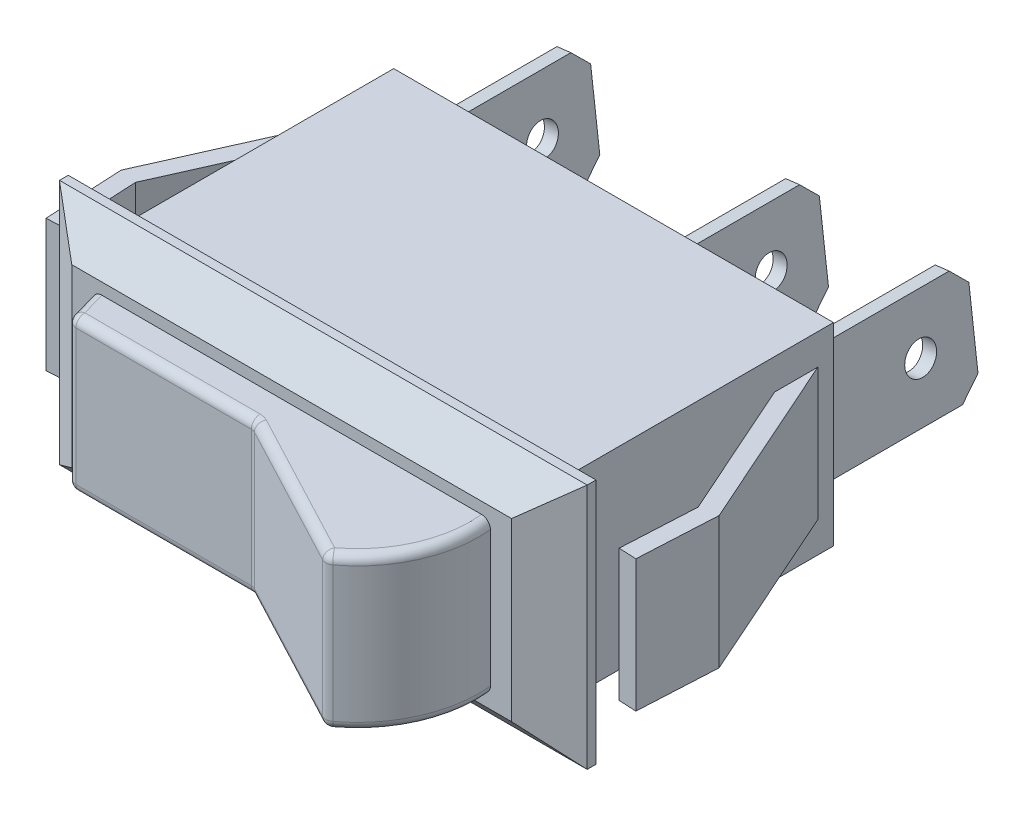
SolidWorks part; units mm, degrees
ref_plane "Front Plane" through (0, 0, 0) normal (0, 0, 1) x (1, 0, 0)
ref_plane "Top Plane" through (0, 0, 0) normal (0, 1, 0) x (1, 0, 0)
ref_plane "Right Plane" through (0, 0, 0) normal (1, 0, 0) x (0, 0, -1)
sketch "Sketch1" plane through (0, 0, 0) normal (0, 0, 1) x (1, 0, 0)
  line L1 (0, 0) -> (25, 0)
  line L2 (0, 0) -> (0, 11)
  line L3 (0, 11) -> (25, 11)
  line L4 (25, 0) -> (25, 11)
  dimension "D1" = 25
  dimension "D2" = 11
extrude "Extrude1" add sketch "Sketch1" along normal blind 16
sketch "Sketch2" plane through (0, 0, 16) normal (0, 0, 1) x (1, 0, 0)
  line L0 (0, 0) -> (25, 0) construction
  line L1 (-2.5, -1.5) -> (27.5, -1.5)
  line L2 (-2.5, -1.5) -> (-2.5, 12.5)
  line L3 (-2.5, 12.5) -> (27.5, 12.5)
  line L4 (27.5, -1.5) -> (27.5, 12.5)
  line L5 (0, 11) -> (0, 0) construction
  dimension "D1" = 30
  dimension "D2" = 14
  dimension "D3" = 1.5
  dimension "D4" = 2.5
extrude "Extrude2" add sketch "Sketch2" along normal blind 2.3
chamfer "Chamfer1" distance 1.8 distance2 2 2 edges at (12.5, 12.5, 18.3) (12.5, -1.5, 18.3)
chamfer "Chamfer2" distance 1.8 distance2 2.5 2 edges at (27.5, 5.5, 18.3) (-2.5, 5.5, 18.3)
ref_plane "Plane1" through (0, 5.5, 0) normal (0, 1, 0) x (-1, 0, 0)
sketch "Sketch4" plane through (0, 5.5, 0) normal (0, 1, 0) x (-1, 0, 0)
  line L0 (0, 0.8928) -> (4.5, 11)
  line L1 (0, 16) -> (0, 0) construction
  line L2 (4.5, 11) -> (4.2642, 15.5)
  line L3 (-25, 0) -> (0, 0) construction
  line L4 (0, 3.3514) -> (3.4888, 11.1874)
  line L5 (3.4888, 11.1874) -> (3.2655, 15.4477)
  line L6 (4.2642, 15.5) -> (3.2655, 15.4477)
  line L7 (0, 0.8928) -> (0, 3.3514)
  line L8 (-0.9135, 1.2996) -> (3.4888, 11.1874) construction
  dimension "D1" = 11
  dimension "D2" = 4.5
  dimension "D3" = 246
  dimension "D4" = 273
  dimension "D5" = 15.5
  dimension "D6" = 1
extrude "Extrude3" add sketch "Sketch4" along normal blind 3.75 and the other way blind 3.75
ref_plane "Plane2" through (12.5, 0, 0) normal (1, 0, 0) x (0, 0, -1)
mirror "Mirror1" about plane through (12.5, 0, 0) normal (1, 0, 0) of "Extrude3"
sketch "Sketch6" plane through (0, 5.5, 0) normal (0, 1, 0) x (-1, 0, 0)
  line L0 (-1.2, 18.3) -> (-1.7107, 20.15)
  line L1 (-25, 18.3) -> (0, 18.3) construction
  line L2 (-1.7107, 20.15) -> (-12.1809, 20.15)
  line L3 (-12.1809, 20.15) -> (-20.7938, 24.7)
  line L4 (-23.8, 18.3) -> (-1.2, 18.3)
  line L5 (-12.5, 6.05) -> (-12.5, -6.05) construction
  line L6 (-25, 16) -> (0, 16) construction
  arc A0 (-20.7938, 24.7) -> (-23.8, 18.3) centre (-16.9254, 18.9769) ccw
  dimension "D1" = 22.6
  dimension "D2" = 11.3
  dimension "D3" = 4.15
  dimension "D4" = 8.7
extrude "Extrude4" add sketch "Sketch6" along normal blind 4.35 and the other way blind 4.35
fillet "Fillet1" radius 0.5 11 edges at (16.4873, 9.85, 22.425) (16.4873, 1.15, 22.425) (23.1778, 1.15, 21.9138) (23.1778, 9.85, 21.9138) (20.7938, 5.5, 24.7) (12.1809, 5.5, 20.15) (6.9458, 1.15, 20.15) (1.4554, 1.15, 19.225) (6.9458, 9.85, 20.15) (1.4554, 9.85, 19.225) (1.7107, 5.5, 20.15)
sketch "Sketch7" plane through (0, 0, 0) normal (0, -1, 0) x (1, 0, 0)
  line L0 (25, 16) -> (25, 0) construction
  line L1 (25, 7.5) -> (0, 7.5)
  line L2 (25, 7.5) -> (25, 5)
  line L3 (25, 5) -> (0, 5)
  line L4 (0, 7.5) -> (0, 5)
  line L5 (0, 16) -> (0, 0) construction
  line L6 (0, 0) -> (25, 0) construction
  dimension "D1" = 2.5
  dimension "D2" = 5
extrude "Cut-Extrude2" cut sketch "Sketch7" against normal blind 0.44
ref_plane "Plane3" through (0, 0, 0) normal (0.9925, 0.1219, 0) x (0, 0, -1)
ref_plane "Plane4" through (1.9851, 0.2437, 0) normal (0.9925, 0.1219, 0) x (0, 0, -1)
sketch "Sketch8" plane through (1.9851, 0.2437, 0) normal (0.9925, 0.1219, 0) x (0, 0, -1)
  line L0 (8.3, 1.9928) -> (9.3, 2.9928)
  line L1 (0.5, 1.9928) -> (8.3, 1.9928)
  line L2 (0, 2.4928) -> (0, 7.7428)
  line L3 (0.5, 8.2428) -> (8.3, 8.2428)
  line L4 (9.3, 2.9928) -> (9.3, 7.2428)
  line L5 (8.3, 8.2428) -> (9.3, 7.2428)
  line L6 (0, 2.4928) -> (0.5, 1.9928)
  line L7 (0, 7.7428) -> (0.5, 8.2428)
  circle A0 centre (6.3, 5.1178) radius 0.9
  point P0 (0, 1.9928)
  point P1 (9.3, 8.2428)
  point P2 (0, 8.2428)
  point P3 (9.3, 1.9928)
  dimension "D3" = 1.8
  dimension "D1" = 9.3
  dimension "D2" = 6.25
  dimension "D4" = 3.125
  dimension "D7" = 3
extrude "Extrude5" add sketch "Sketch8" along normal blind 0.8
pattern_linear "LPattern1" count 2 spacing 13 along (1, 0, 0) of "Extrude5"
pattern_linear "LPattern2" count 2 spacing 21.5 along (1, 0, 0) of "Extrude5"
